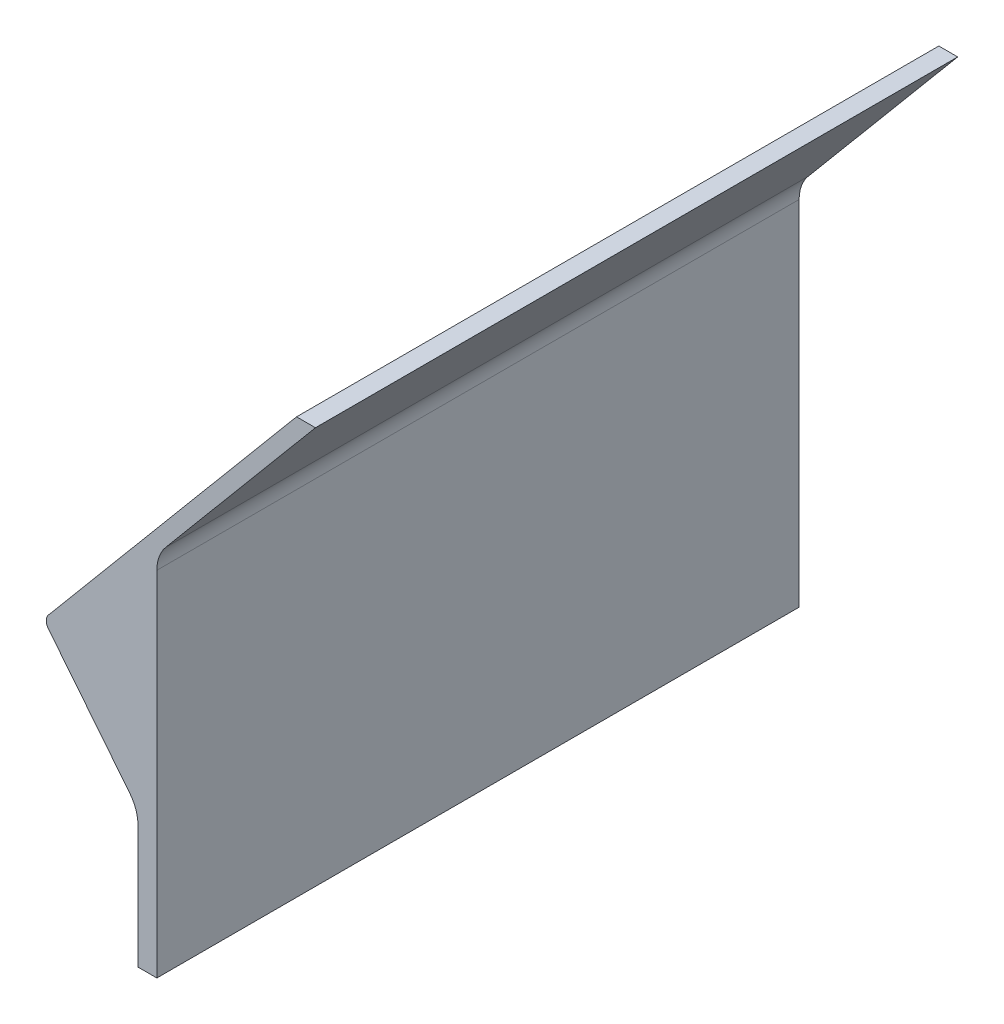
SolidWorks part; units mm, degrees
material "201 Annealed Stainless Steel (SS)"
ref_plane "Front Plane" through (0, 0, 0) normal (0, 0, 1) x (1, 0, 0)
ref_plane "Top Plane" through (0, 0, 0) normal (0, 1, 0) x (1, 0, 0)
ref_plane "Right Plane" through (0, 0, 0) normal (1, 0, 0) x (0, 0, -1)
sketch "Sketch1" plane through (0, 0, 0) normal (0, 0, 1) x (1, 0, 0)
  line L0 (0, 0) -> (0, 97.1)
  line L1 (0, 97.1) -> (41.974, 147.1227)
  line L2 (41.974, 147.1227) -> (36.974, 147.1227)
  line L3 (36.974, 147.1227) -> (-30, 67.3062)
  line L4 (-30, 67.3062) -> (-5, 36.0812)
  line L5 (-5, 36.0812) -> (-5, 0)
  line L6 (-5, 0) -> (0, 0)
  line L7 (-5, 0) -> (-45, 0) construction
  line L8 (-30, 0) -> (-30, 78.9136) construction
  dimension "D1" = 5
  dimension "D2" = 5
  dimension "D3" = 140
  dimension "D4" = 65.3
  dimension "D5" = 97.1
  dimension "D6" = 40
  dimension "D7" = 25
  dimension "D8" = 40
extrude "Funnel - Right Side" add sketch "Sketch1" along normal blind 170
fillet "Fillet2" radius 10 2 edges at (0, 97.1, 85) (-5, 36.0812, 85)
fillet "Fillet3" radius 2.5 1 edges at (-30, 67.3062, 85)
